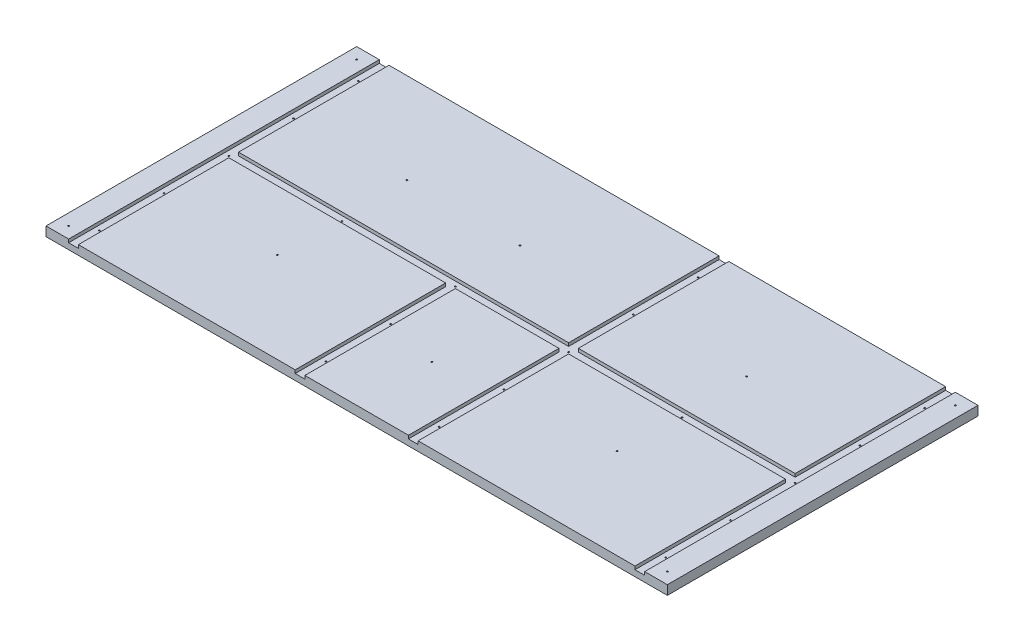
SolidWorks part; units mm, degrees
material "Cedar"
ref_plane "Front Plane" through (0, 0, 0) normal (0, 0, 1) x (1, 0, 0)
ref_plane "Top Plane" through (0, 0, 0) normal (0, 1, 0) x (1, 0, 0)
ref_plane "Right Plane" through (0, 0, 0) normal (1, 0, 0) x (0, 0, -1)
sketch "Sketch1" plane through (0, 0, 0) normal (0, 1, 0) x (1, 0, 0)
  line L1 (-609.6, -304.8) -> (609.6, -304.8)
  line L2 (-609.6, -304.8) -> (-609.6, 304.8)
  line L3 (-609.6, 304.8) -> (609.6, 304.8)
  line L4 (609.6, -304.8) -> (609.6, 304.8)
  line L5 (-609.6, -304.8) -> (609.6, 304.8) construction
  line L6 (-609.6, 304.8) -> (609.6, -304.8) construction
  point P0 (0, 0)
  dimension "D1" = 1219.2
  dimension "D2" = 609.6
extrude "Boss-Extrude1" add sketch "Sketch1" along normal blind 18.2562
sketch "Sketch2" plane through (0, 18.2562, 0) normal (0, 1, 0) x (1, 0, 0)
  line L0 (609.6, 304.8) -> (-609.6, 304.8) construction
  line L1 (-565.15, 304.8) -> (-546.1, 304.8)
  line L2 (-565.15, 304.8) -> (-565.15, -304.8)
  line L3 (-565.15, -304.8) -> (-546.1, -304.8)
  line L4 (-546.1, 304.8) -> (-546.1, 9.525)
  line L5 (-609.6, -304.8) -> (609.6, -304.8) construction
  line L7 (-546.1, 9.525) -> (101.6, 9.525)
  line L8 (-546.1, 9.525) -> (-546.1, -9.525) construction
  line L9 (-546.1, -9.525) -> (-120.65, -9.525)
  line L12 (565.15, 304.8) -> (546.1, 304.8)
  line L13 (565.15, 304.8) -> (565.15, -304.8)
  line L14 (565.15, -304.8) -> (546.1, -304.8)
  line L15 (546.1, 304.8) -> (546.1, 9.525)
  line L17 (-120.65, -9.525) -> (-101.6, -9.525) construction
  line L18 (-120.65, -9.525) -> (-120.65, -304.8)
  line L19 (-120.65, -304.8) -> (-101.6, -304.8)
  line L20 (-101.6, -9.525) -> (-101.6, -304.8)
  line L21 (-546.1, -9.525) -> (-546.1, -304.8)
  line L23 (101.6, -9.525) -> (101.6, -304.8)
  line L24 (101.6, -304.8) -> (120.65, -304.8)
  line L25 (120.65, -9.525) -> (120.65, -304.8)
  line L26 (-101.6, -9.525) -> (101.6, -9.525)
  line L27 (0, 0) -> (0, -9.525) construction
  line L28 (546.1, -9.525) -> (546.1, -304.8)
  line L29 (120.65, -9.525) -> (546.1, -9.525)
  line L30 (-565.15, 304.8) -> (-609.6, 304.8) construction
  line L31 (565.15, 304.8) -> (609.6, 304.8) construction
  line L32 (-609.6, 304.8) -> (-609.6, -304.8) construction
  line L33 (120.65, 9.525) -> (546.1, 9.525)
  line L35 (101.6, 9.525) -> (101.6, 304.8)
  line L36 (101.6, 304.8) -> (120.65, 304.8)
  line L37 (120.65, 9.525) -> (120.65, 304.8)
  line L38 (-546.1, 0) -> (-609.6, 0) construction
  dimension "D1" = 19.05
  dimension "D3" = 425.45
  dimension "D4" = 203.2
  dimension "D5" = 44.45
extrude "Cut-Extrude1" cut sketch "Sketch2" against normal blind 6.35
sketch "Sketch4" plane through (0, 11.9062, 0) normal (0, 1, 0) x (1, 0, 0)
  line L0 (-546.1, -9.525) -> (-546.1, 9.525) construction
  line L1 (-120.65, -9.525) -> (-101.6, -9.525) construction
  line L2 (101.6, -9.525) -> (120.65, -9.525) construction
  line L3 (101.6, 9.525) -> (120.65, 9.525) construction
  line L4 (120.65, 9.525) -> (120.65, 304.8) construction
  line L5 (120.65, 9.525) -> (120.65, 304.8) construction
  line L6 (-565.15, 304.8) -> (-546.1, 304.8) construction
  line L7 (565.15, 304.8) -> (546.1, 304.8) construction
  line L8 (-101.6, -304.8) -> (-120.65, -304.8) construction
  line L9 (120.65, -304.8) -> (101.6, -304.8) construction
  line L10 (120.65, 304.8) -> (101.6, 304.8) construction
  line L11 (120.65, 304.8) -> (101.6, 304.8) construction
  line L12 (-546.1, 0) -> (546.1, 0) construction
  line L13 (0, 0) -> (0, -157.1625) construction
  line L14 (546.1, 9.525) -> (546.1, -9.525) construction
  line L15 (-555.625, 304.8) -> (-555.625, -304.8) construction
  line L16 (-565.15, -304.8) -> (-546.1, -304.8) construction
  line L17 (-587.375, -282.575) -> (-587.375, -304.8) construction
  line L18 (-565.15, 304.8) -> (-609.6, 304.8) construction
  line L19 (-111.125, -304.8) -> (-111.125, -9.525) construction
  line L20 (111.125, -304.8) -> (111.125, -9.525) construction
  line L21 (111.125, 9.525) -> (111.125, 304.8) construction
  line L22 (555.625, 304.8) -> (555.625, -304.8) construction
  line L23 (546.1, -304.8) -> (565.15, -304.8) construction
  line L24 (-587.375, 282.575) -> (-587.375, 304.8) construction
  line L25 (-587.375, 282.575) -> (-609.6, 282.575) construction
  line L26 (-609.6, 304.8) -> (-609.6, -304.8) construction
  line L27 (-609.6, -304.8) -> (-565.15, -304.8) construction
  line L28 (587.375, 282.575) -> (609.6, 282.575) construction
  line L29 (609.6, -304.8) -> (609.6, 304.8) construction
  line L30 (0, -157.1625) -> (-101.6, -157.1625) construction
  line L31 (-101.6, -304.8) -> (-101.6, -9.525) construction
  circle A0 centre (-555.625, 254) radius 1.397
  circle A3 centre (111.125, 254) radius 1.397
  circle A5 centre (555.625, 254) radius 1.397
  circle A6 centre (-333.375, 127) radius 1.397
  circle A7 centre (-111.125, 127) radius 1.397
  circle A8 centre (111.125, 127) radius 1.397
  circle A9 centre (333.375, 127) radius 1.397
  circle A10 centre (555.625, 127) radius 1.397
  circle A11 centre (-333.375, 0) radius 1.397
  circle A12 centre (-111.125, 0) radius 1.397
  circle A13 centre (111.125, 0) radius 1.397
  circle A14 centre (333.375, 0) radius 1.397
  circle A15 centre (555.625, 0) radius 1.397
  circle A16 centre (-333.375, -127) radius 1.397
  circle A17 centre (-111.125, -127) radius 1.397
  circle A18 centre (111.125, -127) radius 1.397
  circle A19 centre (333.375, -127) radius 1.397
  circle A20 centre (555.625, -127) radius 1.397
  circle A22 centre (-111.125, -254) radius 1.397
  circle A23 centre (111.125, -254) radius 1.397
  circle A25 centre (555.625, -254) radius 1.397
  circle A26 centre (-555.625, 127) radius 1.397
  circle A27 centre (-555.625, 0) radius 1.397
  circle A28 centre (-555.625, -127) radius 1.397
  circle A29 centre (-555.625, -254) radius 1.397
  circle A30 centre (-587.375, 282.575) radius 1.397
  circle A31 centre (587.375, 282.575) radius 1.397
  circle A32 centre (587.375, -282.575) radius 1.397
  circle A33 centre (-587.375, -282.575) radius 1.397
  circle A34 centre (-333.375, -254) radius 1.397 [skipped]
  circle A35 centre (333.375, -254) radius 1.397 [skipped]
  circle A36 centre (-333.375, 254) radius 1.397 [skipped]
  circle A37 centre (-111.125, 254) radius 1.397 [skipped]
  circle A38 centre (333.375, 254) radius 1.397 [skipped]
  circle A39 centre (0, -157.1625) radius 1.397
  point P27 (555.625, 304.8)
  point P28 (111.125, 9.525)
  point P29 (111.125, -9.525)
  point P30 (-111.125, -9.525)
  point P31 (-546.1, 0)
  point P32 (-555.625, 304.8)
  point P37 (-111.125, -304.8)
  point P42 (111.125, -304.8)
  point P48 (111.125, 304.8)
  dimension "D1" = 2.794
  dimension "D4" = 127
  dimension "D2" = 6
  dimension "D3" = 5
  dimension "D5" = 2
  dimension "D6" = 2
sketch "Sketch5" plane through (0, 11.9062, 0) normal (0, 1, 0) x (1, 0, 0)
  line L0 (-101.6, -9.525) -> (101.6, -9.525) construction
  point P0 (0, -9.525)
extrude "Cut-Extrude2" cut sketch "Sketch4" against normal through all both and the other way through all
